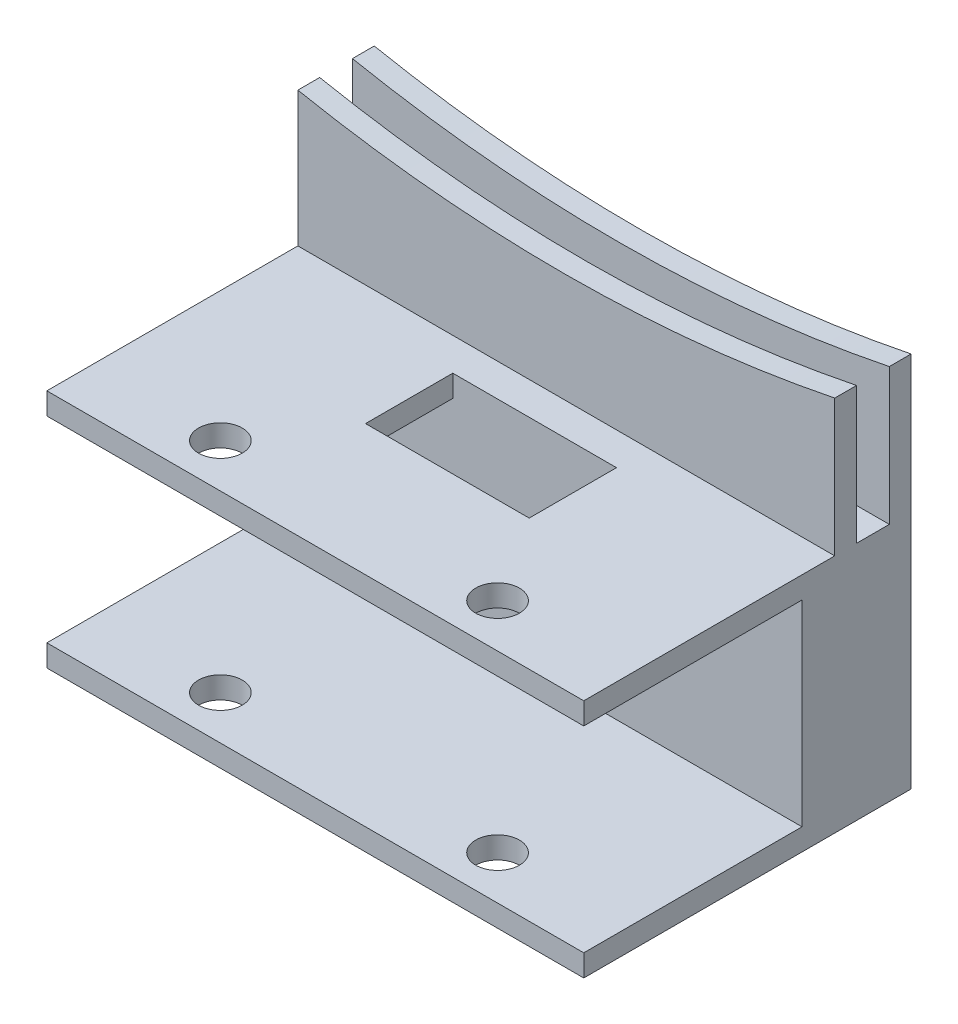
SolidWorks part; units mm, degrees
ref_plane "정면" through (0, 0, 0) normal (0, 0, 1) x (1, 0, 0)
ref_plane "윗면" through (0, 0, 0) normal (0, 1, 0) x (1, 0, 0)
ref_plane "우측면" through (0, 0, 0) normal (1, 0, 0) x (0, 0, -1)
sketch "스케치1" plane through (0, 0, 0) normal (0, 1, 0) x (1, 0, 0)
  line L1 (-23.6243, 20.148) -> (25.5757, 20.148)
  line L2 (-23.6243, 20.148) -> (-23.6243, -9.852)
  line L3 (-23.6243, -9.852) -> (25.5757, -9.852)
  line L4 (25.5757, 20.148) -> (25.5757, -9.852)
  line L5 (-23.6243, 20.148) -> (25.5757, -9.852) construction
  line L6 (-23.6243, -9.852) -> (25.5757, 20.148) construction
  point P0 (0.9757, 5.148)
  dimension "D1" = 49.2
  dimension "D2" = 30
extrude "보스-돌출1" add sketch "스케치1" along normal blind 22
sketch "스케치2" plane through (0, 22, 0) normal (0, 1, 0) x (1, 0, 0)
  line L0 (25.5757, -9.852) -> (25.5757, 20.148) construction
  line L1 (-23.6243, 20.148) -> (25.5757, 20.148)
  line L2 (-23.6243, 20.148) -> (-23.6243, 18.148)
  line L3 (-23.6243, 18.148) -> (25.5757, 18.148)
  line L4 (25.5757, 20.148) -> (25.5757, 18.148)
  line L5 (-23.6243, 20.148) -> (-23.6243, -9.852) construction
  line L6 (25.5757, 15.148) -> (-23.6243, 15.148)
  line L7 (25.5757, 15.148) -> (25.5757, 13.148)
  line L8 (25.5757, 13.148) -> (-23.6243, 13.148)
  line L9 (-23.6243, 15.148) -> (-23.6243, 13.148)
  dimension "D1" = 2
  dimension "D2" = 2
  dimension "D3" = 3
extrude "보스-돌출2" add sketch "스케치2" along normal blind 20
sketch "스케치3" plane through (0, 0, -20.148) normal (0, 0, -1) x (-1, 0, 0)
  line L0 (23.6243, 22) -> (-25.5757, 22) construction
  line L1 (23.6243, 42) -> (23.6243, 0) construction
  line L2 (-25.5757, 42) -> (-25.5757, 0) construction
  line L3 (-25.5757, 42) -> (23.6243, 42) construction
  line L4 (-0.5757, 80.101) -> (-0.5757, 100.101) construction
  line L5 (-25.5757, 42) -> (23.6243, 42)
  line L6 (23.6243, 42) -> (23.6243, 34.3649)
  line L7 (-25.5757, 42) -> (-25.5757, 34.5255)
  arc A0 (23.6243, 34.3649) -> (-25.5757, 34.5255) centre (-0.5757, 157) cw
  dimension "D3" = 125
  dimension "D1" = 20
  dimension "D2" = 135
  dimension "D4" = 0
  dimension "D5" = 25
  dimension "D6" = 0
extrude "컷-돌출1" cut sketch "스케치3" against normal blind 7
sketch "스케치4" plane through (-23.6243, 0, 0) normal (-1, 0, 0) x (0, 0, 1)
  line L0 (9.852, 22) -> (9.852, 0) construction
  line L1 (9.852, 2) -> (-10.148, 2)
  line L2 (9.852, 2) -> (9.852, 20)
  line L3 (9.852, 20) -> (-10.148, 20)
  line L4 (-10.148, 2) -> (-10.148, 20)
  line L5 (-13.148, 22) -> (9.852, 22) construction
  line L6 (-20.148, 0) -> (9.852, 0) construction
  line L7 (-20.148, 34.3649) -> (-20.148, 0) construction
  dimension "D1" = 2
  dimension "D2" = 2
  dimension "D3" = 10
extrude "컷-돌출2" cut sketch "스케치4" against normal blind 50
sketch "스케치5" plane through (0, 0, 0) normal (0, -1, 0) x (1, 0, 0)
  line L0 (25.5757, -10.148) -> (-23.6243, -10.148) construction
  line L1 (25.5757, 9.852) -> (25.5757, -20.148) construction
  line L2 (-23.6243, -20.148) -> (-23.6243, 9.852) construction
  line L3 (25.5757, -20.148) -> (-23.6243, -20.148) construction
  line L4 (25.5757, 5.852) -> (-23.6243, 5.852) construction
  circle A0 centre (13.6757, 5.852) radius 2
  circle A1 centre (-11.7243, 5.852) radius 2
  dimension "D3" = 4
  dimension "D4" = 4
  dimension "D1" = 10
  dimension "D2" = 16
  dimension "D5" = 11.9
  dimension "D6" = 11.9
extrude "컷-돌출3" cut sketch "스케치5" against normal blind 22
sketch "스케치7" plane through (0, 22, 0) normal (0, 1, 0) x (1, 0, 0)
  line L0 (25.5757, 20.148) -> (-23.6243, 20.148) construction
  line L1 (8.5757, 2.148) -> (-6.4243, 2.148)
  line L2 (8.5757, 2.148) -> (8.5757, 10.148)
  line L3 (8.5757, 10.148) -> (-6.4243, 10.148)
  line L4 (-6.4243, 2.148) -> (-6.4243, 10.148)
  line L5 (-23.6243, 13.148) -> (-23.6243, -9.852) construction
  dimension "D1" = 15
  dimension "D2" = 8
  dimension "D3" = 10
  dimension "D4" = 17.2
extrude "컷-돌출4" cut sketch "스케치7" against normal blind 2
